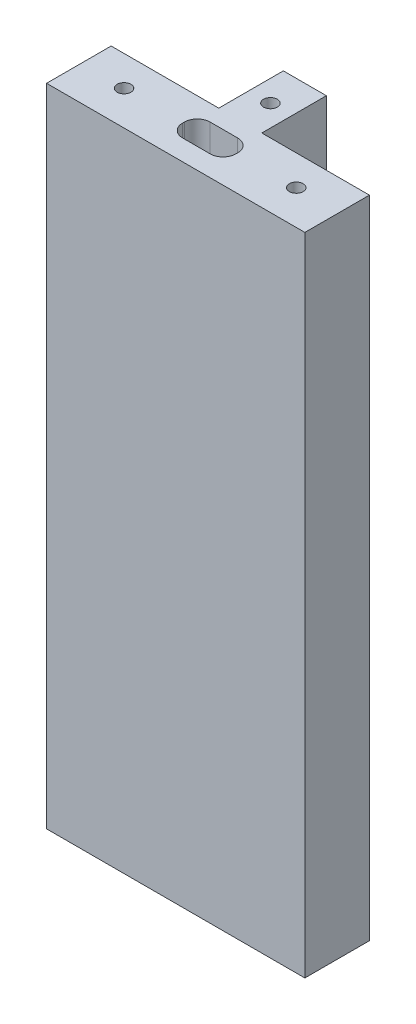
SolidWorks part; units mm, degrees
material "7075-T6 (SN)"
ref_plane "Front Plane" through (0, 0, 0) normal (0, 0, 1) x (1, 0, 0)
ref_plane "Top Plane" through (0, 0, 0) normal (0, 1, 0) x (1, 0, 0)
ref_plane "Right Plane" through (0, 0, 0) normal (1, 0, 0) x (0, 0, -1)
sketch "Sketch1" plane through (0, 0, 0) normal (0, 1, 0) x (1, 0, 0)
  line L0 (-15, 0) -> (15, 0)
  line L1 (15, 0) -> (15, 7.5)
  line L2 (15, 7.5) -> (2.5, 7.5)
  line L3 (2.5, 7.5) -> (2.5, 15)
  line L4 (2.5, 15) -> (-2.5, 15)
  line L5 (-2.5, 15) -> (-2.5, 7.5)
  line L6 (-2.5, 7.5) -> (-15, 7.5)
  line L7 (-15, 7.5) -> (-15, 0)
  dimension "D1" = 30
  dimension "D2" = 15
  dimension "D3" = 7.5
  dimension "D4" = 5
extrude "Boss-Extrude1" add sketch "Sketch1" along normal mid plane 75
sketch "Sketch2" plane through (0, -37.5, 0) normal (0, -1, 0) x (1, 0, 0)
  line L0 (-15, 0) -> (15, 0) construction
  line L1 (-3.1, -2.4) -> (3.1, -2.4)
  line L2 (-3.1, -2.4) -> (-3.1, -5.6)
  line L3 (-3.1, -5.6) -> (3.1, -5.6)
  line L4 (3.1, -2.4) -> (3.1, -5.6)
  point P4 (-3.1, -4)
  point P5 (0, -2.4)
  dimension "D1" = 4
  dimension "D2" = 3.2
  dimension "D3" = 6.2
extrude "Cut-Extrude1" cut sketch "Sketch2" against normal blind 6.2
fillet "Fillet1" radius 1.5 4 edges at (3.1, -34.4, -5.6) (3.1, -34.4, -2.4) (-3.1, -34.4, -5.6) (-3.1, -34.4, -2.4)
hole_wizard "M2 Tapped Hole1" positions "Sketch5" profile "Sketch6" tap size "M2" standard "DIN"
sketch "Sketch5" plane through (0, -37.5, 0) normal (0, -1, 0) x (-1, 0, 0)
  line L0 (-2.5, 15) -> (2.5, 15) construction
  line L1 (15, 0) -> (-15, 0) construction
  point P0 (10, 4)
  point P2 (0, 11)
  point P4 (-10, 4)
  dimension "D1" = 4
  dimension "D2" = 4
  dimension "D3" = 10
  dimension "D4" = 10
sketch "Sketch6" plane through (-10, -37.5, -4) normal (1, 0, 0) x (0, 0, -1)
  line L0 (0, 0) -> (0, 5.6807)
  line L1 (0, 5.6807) -> (0.8, 5.2)
  line L2 (0.8, 5.2) -> (0.8, 0)
  line L5 (0.8, 0) -> (0, 0)
  line L10 (0, 5.6807) -> (-0.8, 5.2) construction
  line L11 (0, -6.35) -> (0, 107.95) construction
  dimension "Tap Drill Dia." = 1.6
  dimension "Tap Drill Depth" = 5.2
  dimension "Drill Angle" = 118
cosmetic thread "Hole Thread1" parameters "D1"=4, "D2"=2
cosmetic thread "Hole Thread2" parameters "D1"=4, "D2"=2
cosmetic thread "Hole Thread3" parameters "D1"=4, "D2"=2
mirror "Mirror1" about plane through (0, 0, 0) normal (0, 1, 0) of "M2 Tapped Hole1", "Fillet1", "Cut-Extrude1"
